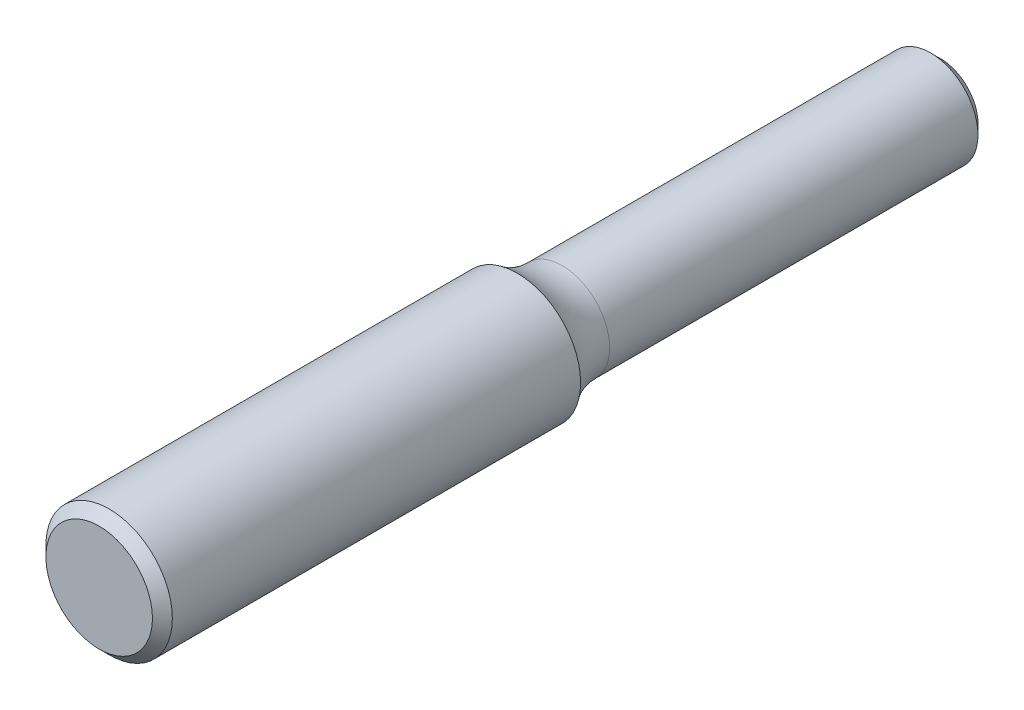
SolidWorks part; units mm, degrees
material "AISI 1020"
ref_plane "Front Plane" through (0, 0, 0) normal (0, 0, 1) x (1, 0, 0)
ref_plane "Top Plane" through (0, 0, 0) normal (0, 1, 0) x (1, 0, 0)
ref_plane "Right Plane" through (0, 0, 0) normal (1, 0, 0) x (0, 0, -1)
sketch "Sketch2" plane through (0, 0, 0) normal (0, 0, 1) x (1, 0, 0)
  circle A0 centre (0, 0) radius 3.175
  dimension "D1" = 6.35
extrude "Boss-Extrude1" add sketch "Sketch2" along normal blind 42.25
sketch "Sketch5" plane through (0, 0, 0) normal (1, 0, 0) x (0, 0, -1)
  line L0 (-42.25, 3.175) -> (-42.25, -3.175) construction
  line L1 (-42.25, 3.175) -> (-42.25, -3.175) construction
  line L2 (-42.25, 0) -> (-21.25, 0) construction
  line L3 (-21.25, 3.175) -> (-21.25, -3.175)
  line L4 (0, 3.175) -> (-42.25, 3.175) construction
  line L5 (-42.25, -3.175) -> (0, -3.175) construction
  line L6 (-21.25, 0) -> (0, 0) construction
  line L7 (0, 3.175) -> (-42.25, 3.175) construction
  line L8 (-19, -3.175) -> (-19, 3.175) construction
  line L9 (-19, 2.3813) -> (-21.25, 2.3813) construction
  line L10 (-19, 2.3813) -> (0, 2.3813)
  line L11 (0, -3.175) -> (0, 3.175) construction
  line L12 (-21.25, 3.175) -> (0, 3.175)
  line L13 (0, 3.175) -> (0, 2.3813)
  arc A0 (-21.25, 3.175) -> (-19, 2.3813) centre (-19, 5.9671) ccw
  point P8 (-19, 0)
  point P11 (-19, 2.3813)
  dimension "D1" = 21
  dimension "D2" = 2.25
  dimension "D3" = 2.3813
revolve "Cut-Revolve1" cut sketch "Sketch5" angle 360 about L6
chamfer "Chamfer1" distance 0.5 angle 45 2 edges at (2.3813, 0, 0) (3.175, 0, 42.25)
